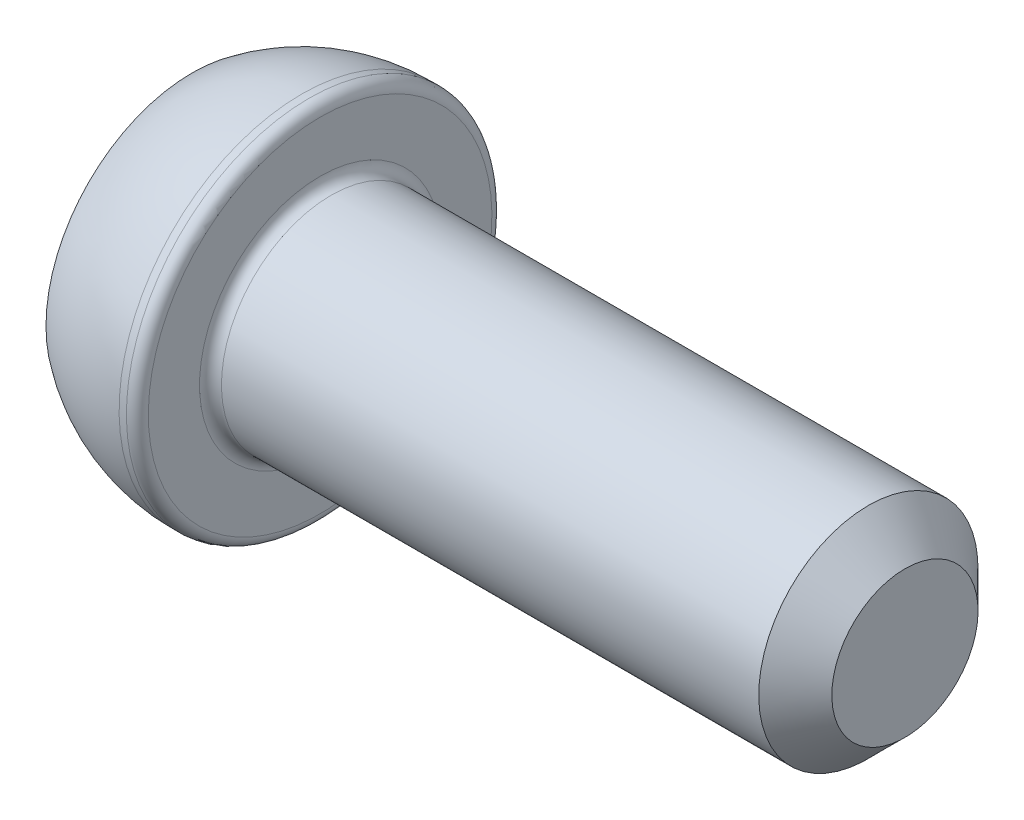
SolidWorks part; units mm, degrees
ref_plane "Спереди" through (0, 0, 0) normal (0, 0, 1) x (1, 0, 0)
ref_plane "Сверху" through (0, 0, 0) normal (0, 1, 0) x (1, 0, 0)
ref_plane "Справа" through (0, 0, 0) normal (1, 0, 0) x (0, 0, -1)
sketch "Эскиз1" plane through (0, 0, 0) normal (0, 0, 1) x (1, 0, 0)
  line L0 (0, 0) -> (0, 4)
  line L1 (3, 5) -> (3.5, 5)
  line L2 (3.5, 5) -> (3.5, 3)
  line L3 (3.5, 3) -> (19.5, 3)
  line L4 (19.5, 3) -> (19.5, 0)
  line L5 (19.5, 0) -> (0, 0) construction
  line L6 (0, 0) -> (19.5, 0)
  arc A0 (0, 4) -> (3, 5) centre (3, 0) cw
  point P9 (3.5, 4)
  dimension "D1" = 0.5
  dimension "D2" = 6
  dimension "D3" = 10
  dimension "D5" = 3.5
  dimension "D6" = 16
revolve "Повернуть1" add sketch "Эскиз1" angle 360 about L5
cosmetic thread "Условное изображение резьбы1" parameters "D2"=4.891
sketch "Эскиз2" plane through (0, 0, 0) normal (-1, 0, 0) x (0, 0, 1)
  line L1 (1.1547, 2) -> (-1.1547, 2)
  line L2 (-1.1547, 2) -> (-2.3094, 0)
  line L3 (-2.3094, 0) -> (-1.1547, -2)
  line L4 (-1.1547, -2) -> (1.1547, -2)
  line L5 (1.1547, -2) -> (2.3094, 0)
  line L6 (2.3094, 0) -> (1.1547, 2)
  circle A0 centre (0, 0) radius 2 construction
  dimension "D1" = 4
extrude "Вырез-Вытянуть1" cut sketch "Эскиз2" against normal blind 2
fillet "Скругление1" radius 0.3 2 edges at (3.5, 3, 0) (3.5, 5, 0)
chamfer "Фаска1" distance 1 angle 45 1 edges at (19.5, 3, 0)
